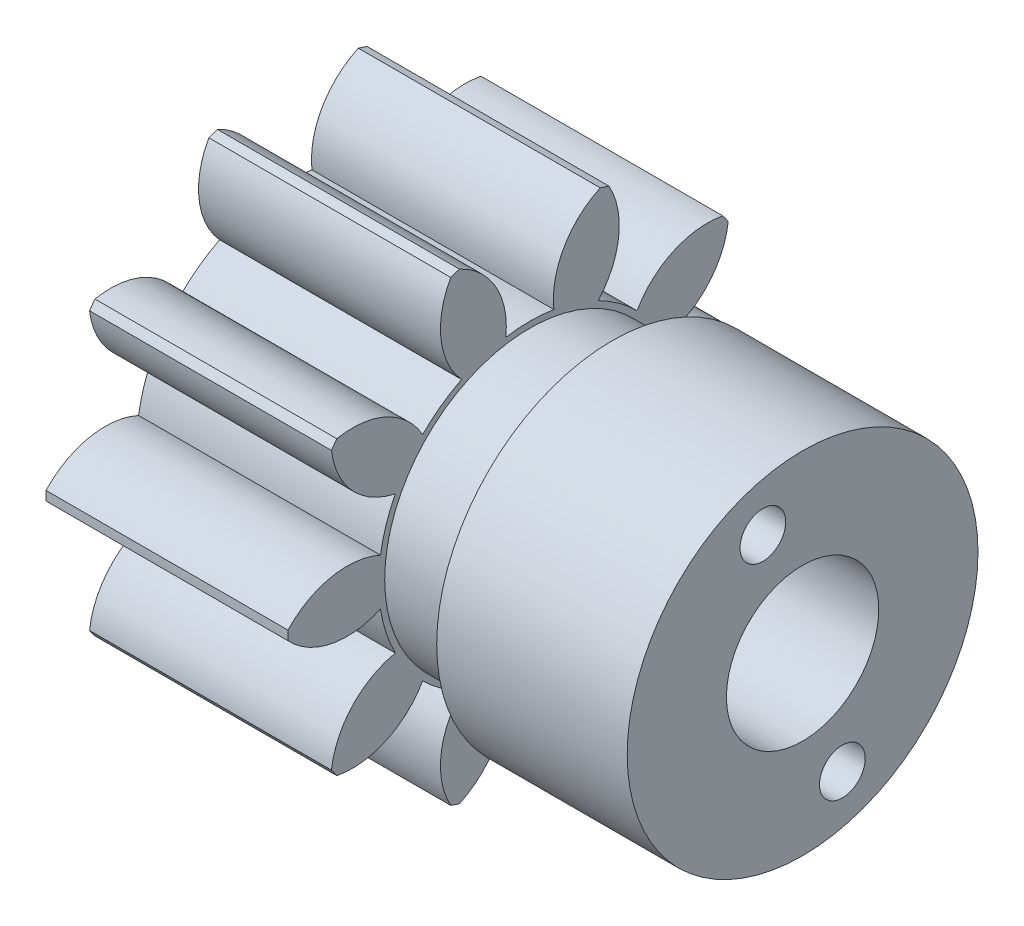
SolidWorks part; units mm, degrees
ref_plane "Plane1" through (0, 0, 0) normal (0, 0, 1) x (1, 0, 0)
ref_plane "Plane2" through (0, 0, 0) normal (0, 1, 0) x (1, 0, 0)
ref_plane "Plane3" through (0, 0, 0) normal (1, 0, 0) x (0, 0, -1)
sketch "HoldingSke" plane through (0, 0, 0) normal (0, 1, 0) x (1, 0, 0)
  line L0 (0, 0) -> (300.1694, -52.928)
  line L1 (-15, 0) -> (100, 0) construction
  line L2 (0, 0) -> (-2.1039, 2.3779)
  line L3 (0, 0) -> (-11.863, 4.5341)
  line L4 (0, 0) -> (8.5048, 1.4996)
  line L5 (0, 0) -> (-47.5972, -17.7524)
  line L6 (0, 0) -> (-10.5278, -7.1032)
  line L7 (-2.1039, 2.3779) -> (8.832, 51.9928)
  line L8 (-76.2, 54.61) -> (-65.4837, 54.61)
  line L9 (-71.009, 38.7566) -> (-53.1078, 45.2721)
  line L10 (-76.2, 71.12) -> (104.1128, 71.12)
  line L11 (0, 0) -> (-12.7, 0)
  line L12 (-76.2, 101.6) -> (-76.1147, 101.6)
  line L13 (24.9733, 27.94) -> (52.9518, 28.4284)
  line L14 (24.9733, 27.94) -> (24.9746, 27.94)
  line L15 (24.9733, 27.94) -> (100.4006, 29.5858)
  circle A0 centre (0, 0) radius 4.7625
  circle A1 centre (0, 0) radius 7.9362
  circle A2 centre (0, 0) radius 38.1
  circle A3 centre (0, 0) radius 4.7625
  dimension "MHD" = 15.8725
  dimension "Hub_dia" = 76.2
  dimension "Bore" = 9.525
  dimension "MBD" = 9.525
  dimension "Num_teeth" = 10
  dimension "Pitch" = 304.8
  dimension "Overall_len" = 50.8
  dimension "Show_teeth" = 10
  dimension "Thickness" = 12.7
  dimension "OAL" = 50.8059
  dimension "T_dim" = 10.7163
  dimension "Ap" = 20
  dimension "H" = 19.05
  dimension "Pitch_radius" = 180.3128
  dimension "Width" = 12.7
  dimension "Backlash" = 0.0853
  dimension "Addendum_fac" = 1
  dimension "Dedendum_fac" = 1.25
  dimension "Clearance_fac" = 0.25
  dimension "Dedendum_add" = 0.0013
sketch "BasProSke" plane through (0, 0, 0) normal (0, 1, 0) x (1, 0, 0)
  line L0 (-10, 0) -> (60, 0) construction
  line L1 (0, 0) -> (0, 12.7)
  line L2 (0, 0) -> (12.7, 0)
  line L3 (12.7, 0) -> (12.7, 12.7)
  line L4 (12.7, 12.7) -> (0, 12.7)
  dimension "Thickness" = 12.7
  dimension "Diameter" = 25.4
revolve "Base-Revolve" add sketch "BasProSke" angle 360 about L0
sketch "TooCutSke" plane through (0, 0, 0) normal (1, 0, 0) x (0, 0, -1)
  line L1 (0, 0) -> (0, 107) construction
  line L2 (0, 0) -> (-1.8046, 10.4283) construction
  line L3 (0, 0) -> (-6.4743, 19.9258) construction
  line L4 (-1.8046, 10.4283) -> (-3.2371, 9.9629) construction
  arc A0 (1.2611, 7.8354) -> (-1.2611, 7.8354) centre (0, 0) ccw
  arc A1 (3.7293, 12.1667) -> (-3.7293, 12.1667) centre (0, 0) ccw
  circle A2 centre (0, 0) radius 10.5833 construction
  circle A3 centre (0, 0) radius 9.9451 construction
  arc A4 (-1.2611, 7.8354) -> (-3.7293, 12.1667) centre (-5.468, 8.3069) ccw
  arc A5 (3.7293, 12.1667) -> (1.2611, 7.8354) centre (5.468, 8.3069) ccw
  dimension "Root_dia" = 15.8725
  dimension "Overcut_dia" = 25.4508
  dimension "Pitch_dia" = 21.1667
  dimension "Base_dia" = 19.8902
  dimension "Flank_rad" = 4.2333
  dimension "Half_ang" = 18
  dimension "Half_CT" = 1.5062
extrude "ToothCut" cut sketch "TooCutSke" along normal through all
fillet "Breaks" [suppressed] radius 0.0423
fillet "RootFillets" [suppressed] radius 0.5304
pattern_circular "TeethCuts" count 10 over 360 about axis through (0, 0, 0) along (1, 0, 0) of "ToothCut", "RootFillets", "Breaks"
sketch "HubNeaOneSke" plane through (0, 0, 0) normal (-1, 0, 0) x (0, 0, 1)
  circle A0 centre (0, 0) radius 7.9362
  dimension "Diameter" = 15.8725
extrude "HubNearOne" [suppressed] add sketch "HubNeaOneSke" along normal blind 38.1059
sketch "HubNeaBotSke" plane through (0, 0, 0) normal (-1, 0, 0) x (0, 0, 1)
  circle A0 centre (0, 0) radius 7.9362
  dimension "Diameter" = 15.8725
extrude "HubNearBoth" [suppressed] add sketch "HubNeaBotSke" along normal blind 19.0529
ref_plane "FarPln" through (12.7, 0, 0) normal (1, 0, 0) x (0, 0, -1)
sketch "HubFarSke" plane through (12.7, 0, 0) normal (1, 0, 0) x (0, 0, -1)
  circle A0 centre (0, 0) radius 7.9362
  dimension "Diameter" = 15.8725
extrude "HubFar" [suppressed] add sketch "HubFarSke" along normal blind 19.0529
sketch "BorSke" plane through (0, 0, 0) normal (1, 0, 0) x (0, 0, -1)
  circle A0 centre (0, 0) radius 4.7625
  dimension "Diameter" = 9.525
extrude "Bore" [suppressed] cut sketch "BorSke" along normal mid plane 101.6118
sketch "KeySke" plane through (0, 0, 0) normal (1, 0, 0) x (0, 0, -1)
  line L0 (-1.1913, 0) -> (-1.1913, 5.9538)
  line L1 (-1.1913, 5.9538) -> (1.1913, 5.9538)
  line L2 (1.1913, 5.9538) -> (1.1913, 0)
  line L3 (0, 0) -> (0, 34) construction
  line L4 (-1.1913, 0) -> (1.1913, 0)
  dimension "Offset" = 5.9538
  dimension "Width" = 2.3825
extrude "Keyway" [suppressed] cut sketch "KeySke" along normal mid plane 101.6118
pattern_circular "Keyway2" [suppressed] count 2 every 90 about axis through (-10, 0, 0) along (1, 0, 0)
sketch "Sketch1" [suppressed] plane through (12.7, 0, 0) normal (1, 0, 0) x (0, 0, -1)
  circle A0 centre (0, 0) radius 7.9362
  circle A1 centre (0, 0) radius 4.7625 construction
  circle A2 centre (0, 0) radius 4.7625
sketch "Sketch2" plane through (12.7, 0, 0) normal (1, 0, 0) x (0, 0, -1)
  line L11 (-15.875, -15.875) -> (15.875, -15.875)
  line L12 (-15.875, -15.875) -> (-15.875, 15.875)
  line L13 (-15.875, 15.875) -> (15.875, 15.875)
  line L14 (15.875, -15.875) -> (15.875, 15.875)
  line L15 (-15.875, -15.875) -> (15.875, 15.875) construction
  line L16 (-15.875, 15.875) -> (15.875, -15.875) construction
  point P0 (0, 0)
  dimension "D1" = 31.75
hole_wizard "CBORE for 1/4 Socket Head Cap Screw1" [suppressed] positions "Sketch3" profile "Sketch5" counterbore size "1/4" standard "ANSI Inch"
sketch "Sketch3" plane through (9.525, 0, 0) normal (1, 0, 0) x (0, 0, -1)
  point P0 (-15.875, 15.875)
  point P3 (15.875, 15.875)
  point P6 (15.875, -15.875)
  point P9 (-15.875, -15.875)
sketch "Sketch5" plane through (9.525, 15.875, 15.875) normal (0, 1, 0) x (0, 0, -1)
  line L0 (0, 0) -> (0, 9.525)
  line L1 (0, 9.525) -> (3.5712, 9.525)
  line L3 (3.5712, 9.525) -> (3.5712, 6.35)
  line L4 (3.5712, 6.35) -> (5.5562, 6.35)
  line L5 (5.5562, 6.35) -> (5.5563, 0)
  line L7 (5.5563, 0) -> (0, 0)
  line L11 (0, -6.35) -> (0, 107.95) construction
  dimension "Thru Hole Dia." = 7.1425
  dimension "Thru Hole Depth" = 9.525
  dimension "C'Bore Dia." = 11.1125
  dimension "C'Bore Depth" = 6.35
inserted part "uxcell-FR6ZZ" [suppressed]
move or copy body "Body-Move/Copy2" [suppressed] placed by mates yes
combine bodies "Combine1" [suppressed] operation type subtract main body 105 bodies to subtract 107
hole_wizard "3/8 Clearance Hole1" [suppressed] positions "Sketch6" profile "Sketch7" hole size "3/8" standard "ANSI Inch"
sketch "Sketch6" plane through (9.525, 0, 0) normal (1, 0, 0) x (0, 0, -1)
  point P0 (0, 0)
sketch "Sketch7" plane through (9.525, 0, 0) normal (0, 1, 0) x (0, 0, -1)
  line L0 (0, 0) -> (0, 9.525)
  line L1 (0, 9.525) -> (6.985, 9.525)
  line L2 (6.985, 9.525) -> (6.985, 0)
  line L5 (6.985, 0) -> (0, 0)
  line L11 (0, -6.35) -> (0, 107.95) construction
  dimension "Thru Hole Dia." = 13.97
  dimension "Thru Hole Depth" = 9.525
sketch "Sketch15" plane through (12.7, 0, 0) normal (1, 0, 0) x (0, 0, -1)
  circle A0 centre (0, 0) radius 7.62
  dimension "D1" = 15.24
extrude "Boss-Extrude2" add sketch "Sketch15" along normal blind 4.318
sketch "Sketch8" plane through (17.018, 0, 0) normal (1, 0, 0) x (0, 0, -1)
  circle A0 centre (0, 0) radius 9.2075
  dimension "D1" = 18.415
extrude "Boss-Extrude1" add sketch "Sketch8" along normal blind 10
sketch "Sketch9" plane through (27.018, 0, 0) normal (1, 0, 0) x (0, 0, -1)
  line L0 (-5.348, 5.3597) -> (1.1763, 7.4796) construction
  line L1 (-2.0859, 6.4196) -> (0, 0) construction
  arc A0 (-3.6944, 12.1508) -> (-4.1532, 12.0017) centre (0, 0) ccw construction
  point P12 (-3.9245, 12.0784)
  dimension "D1" = 6.75
  dimension "D2" = 6.86
hole_wizard "M2 Clearance Hole1" positions "Sketch10" profile "Sketch11" hole size "M2" standard "ANSI Metric"
sketch "Sketch10" plane through (27.018, 0, 0) normal (1, 0, 0) x (0, 0, -1)
  point P4 (-2.0859, 6.4196)
sketch "Sketch11" plane through (27.018, 6.4196, 2.0859) normal (0, 1, 0) x (0, 0, -1)
  line L0 (0, 0) -> (0, 10.721)
  line L1 (0, 10.721) -> (1.2, 10)
  line L2 (1.2, 10) -> (1.2, 0)
  line L5 (1.2, 0) -> (0, 0)
  line L10 (0, 10.721) -> (-1.2, 10) construction
  line L11 (0, -6.35) -> (0, 107.95) construction
  dimension "Hole Dia." = 2.4
  dimension "Hole Depth" = 10
  dimension "Drill Angle" = 118
pattern_circular "CirPattern1" count 4 over 360 about axis through (27.018, 0, 0) along (-1, 0, 0) skipping 1, 3 of "M2 Clearance Hole1"
sketch "Pitch Circle" plane through (0, 0, 0) normal (1, 0, 0) x (0, 0, -1)
  circle A0 centre (0, 0) radius 10.5833 construction
  circle A1 centre (0, 0) radius 10.5833
sketch "Sketch13" plane through (0, 0, 0) normal (-1, 0, 0) x (0, 0, 1)
  circle A0 centre (0, 0) radius 4
  dimension "D1" = 8
extrude "Cut-Extrude1" cut sketch "Sketch13" against normal through all both and the other way through all
equation "' \"Pitch@HoldingSke\" = 4"
equation "' \"Num_teeth@HoldingSke\" = 12"
equation "' \"Ap@HoldingSke\" =  20"
equation "' \"Ap@HoldingSke\" = 20"
equation "' \"Width@HoldingSke\" = 0.5"
equation "' \"Hub_dia@HoldingSke\"= 1"
equation "' \"Hub_dia@HoldingSke\" = 1"
equation "' \"Overall_len@HoldingSke\" = 1.0"
equation "' \"Bore@HoldingSke\" = 0.75"
equation "' \"T_dim@HoldingSke\" = 0.85"
equation "' \"Width@KeySke\" = 0.25"
equation "' \"Show_teeth@HoldingSke\" = 13"
equation "' \"Backlash@HoldingSke\" = 0.009"
equation "' \"Addendum_fac@HoldingSke\" = 1.0"
equation "' \"Dedendum_fac@HoldingSke\" = 1.25"
equation "' \"Dedendum_add@HoldingSke\" = 0.00005"
equation "' \"Clearance_fac@HoldingSke\" = 0.25"
equation "' \"Pitch@HoldingSke\" = 0.5"
equation "' \"Num_teeth@HoldingSke\" = 23"
equation "' \"Show_teeth@HoldingSke\" = 23"
equation "' \"Backlash@HoldingSke\" = 0.0375"
equation "\"Overcut_dia@TooCutSke\" = (\"Num_teeth@HoldingSke\" + 2 * \"Addendum_fac@HoldingSke\") / \"Pitch@HoldingSke\" + 0.002"
equation "\"Pitch_dia@TooCutSke\"= \"Num_teeth@HoldingSke\" / \"Pitch@HoldingSke\""
equation "\"Base_dia@TooCutSke\" = \"Num_teeth@HoldingSke\" / \"Pitch@HoldingSke\" * cos((\"Ap@HoldingSke\"  * 3.14159265 / 180))"
equation "\"Root_dia@TooCutSke\" = (\"Num_teeth@HoldingSke\" + 2) / \"Pitch@HoldingSke\" - 2 * (\"Addendum_fac@HoldingSke\" + \"Dedendum_fac@HoldingSke\") / \"Pitch@HoldingSke\" - \"Dedendum_add@HoldingSke\" * 2"
equation "\"Half_ang@TooCutSke\" = 180 / \"Num_teeth@HoldingSke\""
equation "\"Half_CT@TooCutSke\" = \"Num_teeth@HoldingSke\" / \"Pitch@HoldingSke\" * sin((3.14159265 / 2 / \"Num_teeth@HoldingSke\")) / 2 - 7 * \"Backlash@HoldingSke\" / 4"
equation "\"Flank_rad@TooCutSke\" = \"Num_teeth@HoldingSke\" / \"Pitch@HoldingSke\" / 5"
equation "\"Radius@RootFillets\" = \"Clearance_fac@HoldingSke\" / \"Pitch@HoldingSke\" + \"Dedendum_add@HoldingSke\""
equation "\"Break_rad@Breaks\" = 0.02 / \"Pitch@HoldingSke\""
equation "\"Thickness@HoldingSke\" = \"Width@HoldingSke\""
equation "\"OAL@HoldingSke\" = \"Thickness@HoldingSke\""
equation "\"MHD@HoldingSke\" = (\"Num_teeth@HoldingSke\" + 2) / \"Pitch@HoldingSke\" - 2 * (\"Addendum_fac@HoldingSke\" + \"Dedendum_fac@HoldingSke\")  / \"Pitch@HoldingSke\" - \"Dedendum_add@HoldingSke\" * 2"
equation "\"MBD@HoldingSke\" = (\"Num_teeth@HoldingSke\" + 2) / \"Pitch@HoldingSke\" - 2 * (\"Addendum_fac@HoldingSke\" + \"Dedendum_fac@HoldingSke\")  / \"Pitch@HoldingSke\" - \"Dedendum_add@HoldingSke\" * 2 - 0.002"
equation "\"MHD@HoldingSke\" = ((sgn( \"MHD@HoldingSke\" - \"Hub_dia@HoldingSke\" )-1)*( \"MHD@HoldingSke\" - \"Hub_dia@HoldingSke\" ))/-2+ \"Hub_dia@HoldingSke\""
equation "\"MBD@HoldingSke\" = ((sgn( \"MBD@HoldingSke\" - \"Bore@HoldingSke\" )-1)*( \"MBD@HoldingSke\" - \"Bore@HoldingSke\" ))/-2+ \"Bore@HoldingSke\""
equation "\"OAL@HoldingSke\" = ((sgn( \"OAL@HoldingSke\" - \"Overall_len@HoldingSke\" )+1)*( \"OAL@HoldingSke\" - \"Overall_len@HoldingSke\" ))/2 + \"Overall_len@HoldingSke\" + 0.000002"
equation "\"Num_teeth@TeethCuts\" = int( \"Show_teeth@HoldingSke\" ) + 1"
equation "\"Num_teeth@TeethCuts\" = ((sgn( \"Num_teeth@TeethCuts\" - \"Num_teeth@HoldingSke\" )-1)*( \"Num_teeth@TeethCuts\" - \"Num_teeth@HoldingSke\" ))/-2+ \"Num_teeth@HoldingSke\""
equation "\"Num_teeth@TeethCuts\" = ((sgn( \"Num_teeth@TeethCuts\" - 2.0)+1)*( \"Num_teeth@TeethCuts\" - 2.0))/2 +2.0"
equation "\"Angle@TeethCuts\" = 360.0 / \"Num_teeth@HoldingSke\""
equation "\"Diameter@BasProSke\" = (\"Num_teeth@HoldingSke\" + 2 * \"Addendum_fac@HoldingSke\") / \"Pitch@HoldingSke\""
equation "\"Thickness@BasProSke\"  = \"Thickness@HoldingSke\""
equation "' \"Fillet_rad@BasProSke\" =  \"Thickness@HoldingSke\" * 0.05"
equation "' \"Fillet_rad@BasProSke\" = \"Thickness@HoldingSke\" * 0.05"
equation "\"MHD@HoldingSke\" = ((sgn( \"MHD@HoldingSke\" - \"Root_dia@TooCutSke\" )-1)*( \"MHD@HoldingSke\" - \"Root_dia@TooCutSke\" ))/-2+ \"Root_dia@TooCutSke\""
equation "\"Diameter@HubNeaOneSke\" = \"MHD@HoldingSke\""
equation "\"Length@HubNearOne\" = \"OAL@HoldingSke\" - \"Thickness@BasProSke\""
equation "\"Diameter@HubNeaBotSke\" = \"MHD@HoldingSke\""
equation "\"Length@HubNearBoth\" = ( \"OAL@HoldingSke\" - \"Thickness@BasProSke\" ) / 2.0"
equation "\"Thickness@FarPln\" = \"Thickness@BasProSke\""
equation "\"Diameter@HubFarSke\" = \"MHD@HoldingSke\""
equation "\"Length@HubFar\" = ( \"OAL@HoldingSke\" - \"Thickness@BasProSke\" ) / 2.0"
equation "\"Diameter@BorSke\" = \"MBD@HoldingSke\""
equation "\"D1@Bore\" = \"OAL@HoldingSke\" * 2.0"
equation "\"D1@Keyway\" = \"OAL@HoldingSke\" * 2.0"
equation "\"Offset@KeySke\" = \"T_dim@HoldingSke\" - \"MBD@HoldingSke\" / 2.0"
